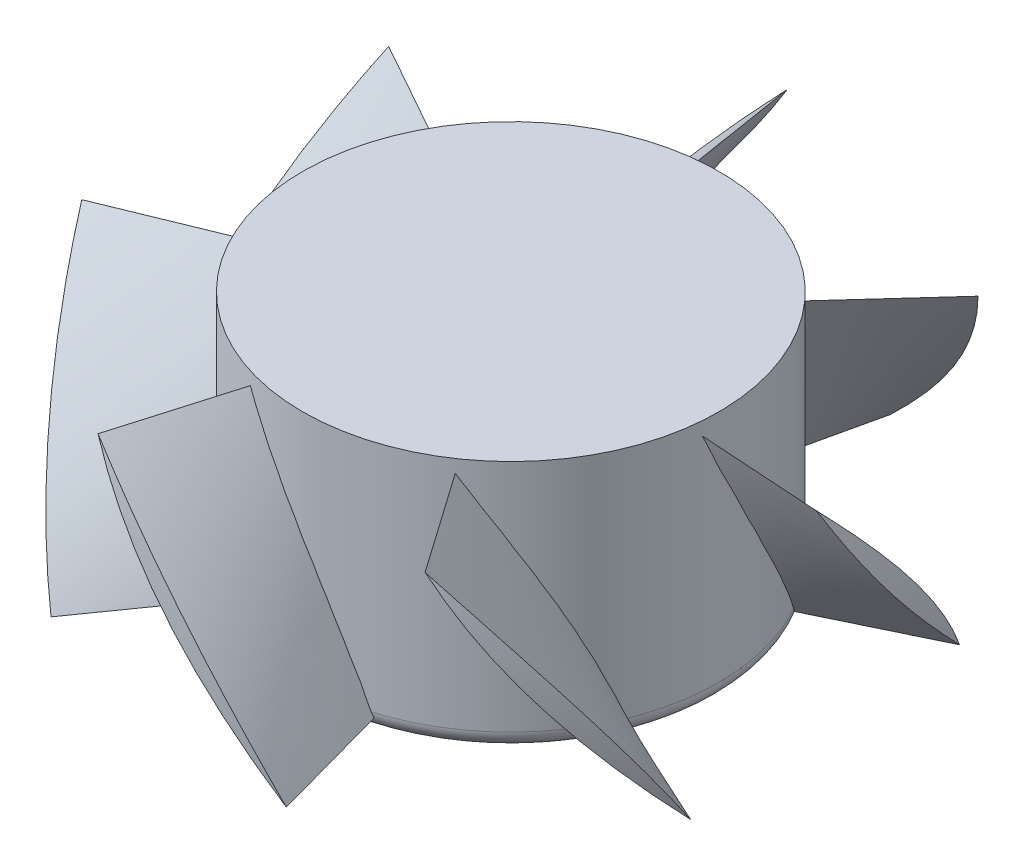
SolidWorks part; units mm, degrees
ref_plane "Frontale" through (0, 0, 0) normal (0, 0, 1) x (1, 0, 0)
ref_plane "Superiore" through (0, 0, 0) normal (0, 1, 0) x (1, 0, 0)
ref_plane "Destro" through (0, 0, 0) normal (1, 0, 0) x (0, 0, -1)
sketch "Schizzo1" plane through (0, 0, 0) normal (0, 1, 0) x (-1, 0, 0)
  circle A0 centre (0, 0) radius 17.5
  dimension "D1" = 35
extrude "Estrusione-Estrusione1" add sketch "Schizzo1" along normal blind 9 and the other way blind 12.2
ref_plane "Piano1" through (0, 0, 16) normal (0, 0, 1) x (1, 0, 0)
ref_plane "Piano2" through (0, 0, 29) normal (0, 0, 1) x (1, 0, 0)
sketch "Schizzo4" plane through (0, 0, 16) normal (0, 0, 1) x (1, 0, 0)
  line L0 (-17.5, -12.2) -> (17.5, -12.2) construction
  line L1 (17.5, 9) -> (-17.5, 9) construction
  spline S0 degree 2 poles (-5, 7.9) (-0.5195, -1.8723) (5, -11.1) knots 0 0 0 1 1 1
  spline S1 degree 2 poles (-5, 7.9) (1.3354, -0.8812) (5, -11.1) knots 0 0 0 1 1 1
  dimension "D1" = 5
  dimension "D2" = 5
  dimension "D3" = 1.1
  dimension "D4" = 1.1
sketch "Schizzo5" plane through (0, 0, 29) normal (0, 0, 1) x (1, 0, 0)
  spline S0 degree 2 poles (-8.8372, 7.877) (0.6858, -0.9443) (8.3722, -11.394) knots 0 0 0 1 1 1
  spline S2 degree 2 poles (-8.8372, 7.877) (-1.7254, -3.0694) (8.3722, -11.394) knots 0 0 0 1 1 1
loft "Loft1" add profiles "Schizzo5", "Schizzo4"
ref_plane "Piano3" through (12, 0, 0) normal (1, 0, 0) x (0, 0, -1)
sketch "Schizzo9" plane through (12, 0, 0) normal (1, 0, 0) x (0, 0, -1)
  line L0 (-29.1149, 9.1377) -> (-26.3149, 9.1377)
  line L1 (-29.1149, -12.8623) -> (-26.3149, -12.8623)
  line L2 (-29.1149, 9.1377) -> (-29.1149, -12.8623)
  arc A0 (-26.3149, -12.8623) -> (-26.3149, 9.1377) centre (22.9725, -1.8623) cw
  point P8 (-27.5275, -1.8623)
  dimension "D4" = 50.5
  dimension "D1" = 22
  dimension "D2" = 2.8
  dimension "D3" = 2.8
extrude "Taglio-Estrusione2" cut sketch "Schizzo9" against normal blind 25
pattern_circular "RipetizioneCircolare7" count 7 over 360 about axis through (0, 9, 0) along (0, 1, 0) of bodies 106
fillet "Raccordo1" radius 1.5 1 edges at (0, -12.2, 17.5)
